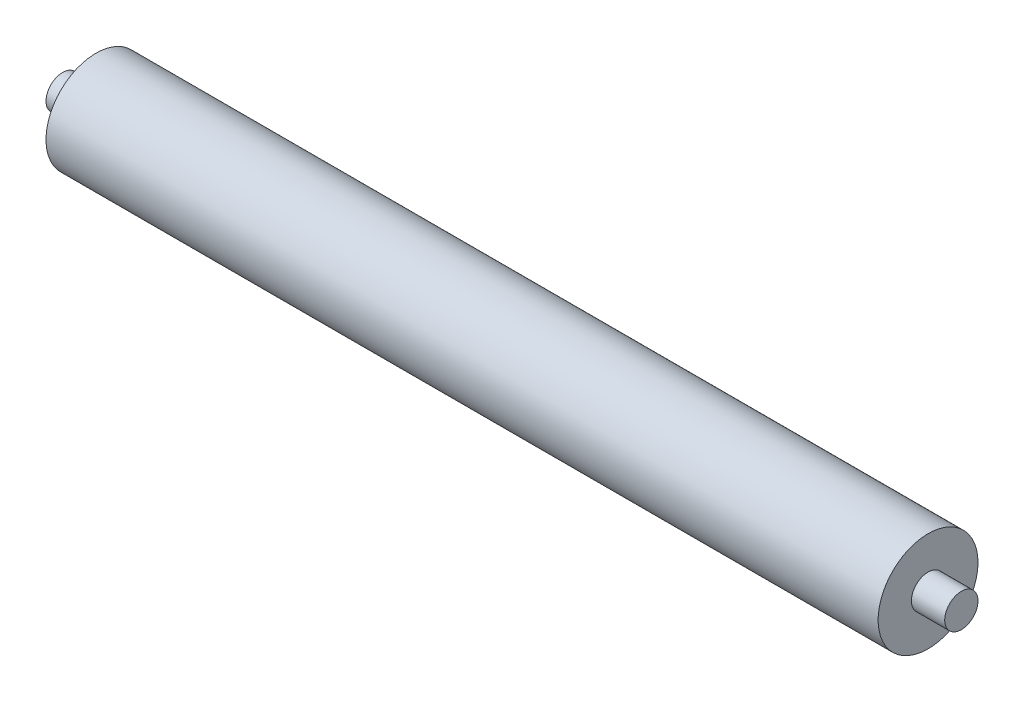
SolidWorks part; units mm, degrees
ref_plane "Alzado" through (0, 0, 0) normal (0, 0, 1) x (1, 0, 0)
ref_plane "Planta" through (0, 0, 0) normal (0, 1, 0) x (1, 0, 0)
ref_plane "Vista lateral" through (0, 0, 0) normal (1, 0, 0) x (0, 0, -1)
sketch "Croquis1" plane through (0, 0, 0) normal (1, 0, 0) x (0, 0, -1)
  circle A0 centre (0, 0) radius 1.5
  dimension "D1" = 3
extrude "Saliente-Extruir1" add sketch "Croquis1" along normal blind 25
sketch "Croquis2" plane through (25, 0, 0) normal (1, 0, 0) x (0, 0, -1)
  circle A0 centre (0, 0) radius 0.5
  dimension "D1" = 1
extrude "Saliente-Extruir2" add sketch "Croquis2" along normal blind 1
sketch "Croquis3" plane through (0, 0, 0) normal (-1, 0, 0) x (0, 0, 1)
  circle A0 centre (0, 0) radius 0.5
  dimension "D1" = 1
extrude "Saliente-Extruir3" add sketch "Croquis3" along normal blind 1
